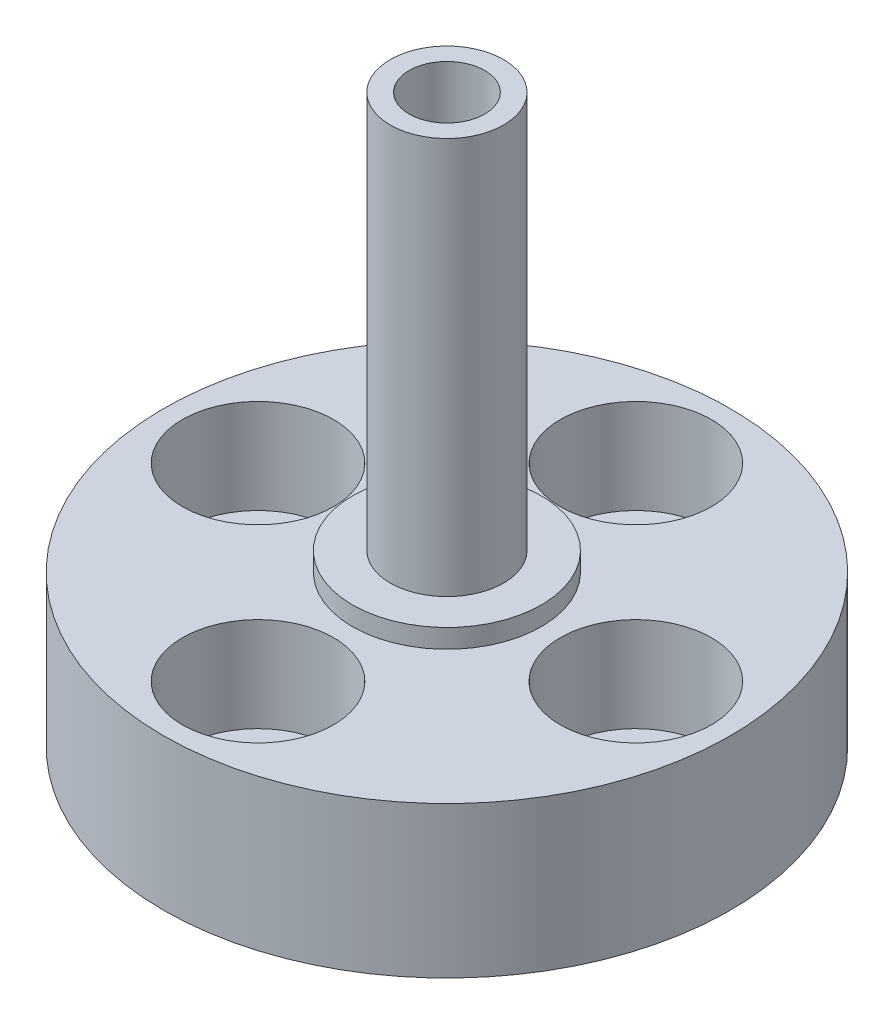
SolidWorks part; units mm, degrees
ref_plane "Front Plane" through (0, 0, 0) normal (0, 0, 1) x (1, 0, 0)
ref_plane "Top Plane" through (0, 0, 0) normal (0, 1, 0) x (1, 0, 0)
ref_plane "Right Plane" through (0, 0, 0) normal (1, 0, 0) x (0, 0, -1)
sketch "Sketch1" plane through (0, 0, 0) normal (0, 1, 0) x (1, 0, 0)
  circle A0 centre (0, 0) radius 15
  dimension "D1" = 30
extrude "Boss-Extrude1" add sketch "Sketch1" along normal blind 8
sketch "Sketch2" plane through (0, 8, 0) normal (0, 1, 0) x (1, 0, 0)
  circle A0 centre (0, 0) radius 5
  dimension "D1" = 10
extrude "Boss-Extrude2" add sketch "Sketch2" along normal blind 1
sketch "Sketch3" plane through (0, 9, 0) normal (0, 1, 0) x (1, 0, 0)
  circle A0 centre (0, 0) radius 3
  dimension "D1" = 6
extrude "Boss-Extrude3" add sketch "Sketch3" along normal blind 21
hole_wizard "Hole1" positions "Sketch7" profile "Sketch6" legacy end condition through all
sketch "Sketch7" plane through (0, 8, 0) normal (0, 1, 0) x (1, 0, 0)
  point P0 (-10, 0)
  point P2 (0, 10)
  point P4 (10, 0)
  point P6 (0, -10)
  dimension "D1" = 10
  dimension "D2" = 10
  dimension "D3" = 10
  dimension "D4" = 10
sketch "Sketch6" plane through (-10, 8, 0) normal (1, 0, 0) x (0, 0, 1)
  line L0 (0, 0) -> (0, 8)
  line L1 (0, 8) -> (2, 8)
  line L2 (2, 8) -> (2, 5)
  line L3 (2, 5) -> (4, 5)
  line L4 (4, 5) -> (4, 0)
  line L5 (4, 0) -> (0, 0)
  line L6 (0, 110) -> (0, -10) construction
  dimension "Diameter" = 4
  dimension "Depth" = 8
  dimension "C-Bore Diameter" = 8
  dimension "C-Bore Depth" = 5
sketch "Sketch8" plane through (0, 30, 0) normal (0, 1, 0) x (1, 0, 0)
  circle A0 centre (0, 0) radius 2
  dimension "D1" = 4
extrude "Cut-Extrude1" cut sketch "Sketch8" against normal blind 12
